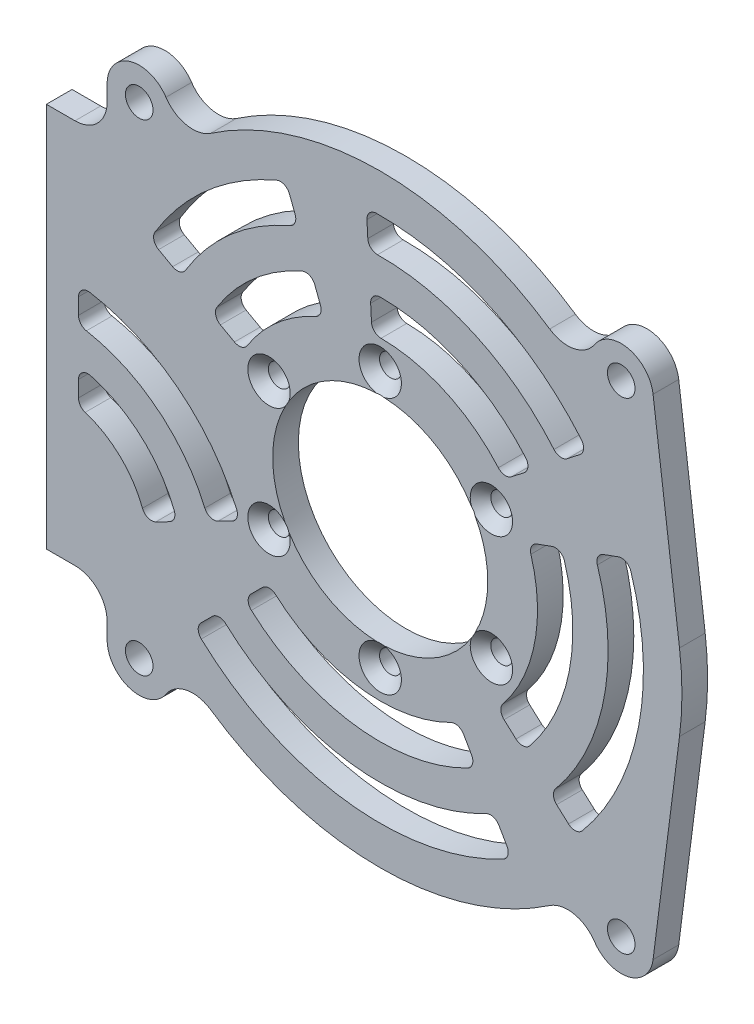
SolidWorks part; units mm, degrees
material "Thornel Mat VMA"
ref_plane "前视基准面" through (0, 0, 0) normal (0, 0, 1) x (1, 0, 0)
ref_plane "上视基准面" through (0, 0, 0) normal (0, 1, 0) x (1, 0, 0)
ref_plane "右视基准面" through (0, 0, 0) normal (1, 0, 0) x (0, 0, -1)
sketch "草图1" plane through (0, 0, 0) normal (0, 0, 1) x (1, 0, 0)
  line L0 (0, 0) -> (50000, 0) construction
  line L1 (-52, 8.75) -> (-52, -8.75)
  line L2 (-52, 8.75) -> (-52, 30)
  line L3 (-52, -8.75) -> (-52, -30)
  line L6 (-42.54, 37.5) -> (-42.54, 35)
  line L7 (-47.54, 30) -> (-52, 30)
  line L8 (-47.54, -30) -> (-52, -30)
  line L9 (-42.54, -37.5) -> (-42.54, -35)
  line L10 (0, 0) -> (0, -50000) construction
  line L11 (42.4995, 38.1352) -> (46.6192, 5.9711)
  line L12 (42.4995, -38.1352) -> (46.6192, -5.9711)
  circle A2 centre (-37.54, 37.5) radius 2.15
  circle A3 centre (-37.54, -37.5) radius 2.15
  arc A4 (-33.3722, 40.2622) -> (-42.54, 37.5) centre (-37.54, 37.5) ccw
  arc A5 (-42.54, -37.5) -> (-33.3722, -40.2622) centre (-37.54, -37.5) ccw
  arc A6 (-26.3963, -38.8874) -> (26.3963, -38.8874) centre (0, 0) ccw
  arc A7 (-33.3722, 40.2622) -> (-26.3963, 38.8874) centre (-29.2045, 43.0244) ccw
  arc A8 (-33.3722, -40.2622) -> (-42.54, -37.5) centre (-37.54, -37.5) cw
  arc A9 (-33.3722, -40.2622) -> (-26.3963, -38.8874) centre (-29.2045, -43.0244) cw
  circle A10 centre (37.54, -37.5) radius 2.15
  circle A11 centre (37.54, 37.5) radius 2.15
  arc A12 (42.4995, 38.1352) -> (33.3722, 40.2622) centre (37.54, 37.5) ccw
  arc A13 (33.3722, -40.2622) -> (42.4995, -38.1352) centre (37.54, -37.5) ccw
  arc A14 (33.3722, 40.2622) -> (26.3963, 38.8874) centre (29.2045, 43.0244) cw
  arc A15 (33.3722, -40.2622) -> (26.3963, -38.8874) centre (29.2045, -43.0244) ccw
  arc A16 (26.3963, 38.8874) -> (-26.3963, 38.8874) centre (0, 0) ccw
  arc A17 (46.6192, -5.9711) -> (46.6192, 5.9711) centre (0, 0) ccw
  arc A18 (-47.54, -30) -> (-42.54, -35) centre (-47.54, -35) cw
  arc A19 (-42.54, 35) -> (-47.54, 30) centre (-47.54, 35) cw
  point P8 (-52, 0)
  point P44 (-42.54, -30)
  point P47 (-42.54, 30)
  dimension "D5" = 4.3
  dimension "D6" = 75
  dimension "D8" = 10
  dimension "D9" = 94
  dimension "D10" = 5
  dimension "D11" = 10
  dimension "D12" = 5
  dimension "D13" = 5
  dimension "D14" = 5
  dimension "D2" = 17.5
  dimension "D3" = 52
  dimension "D4" = 60
  dimension "D7" = 14.46
extrude "凸台-拉伸1" add sketch "草图1" along normal blind 4
sketch "草图2" plane through (0, 0, 4) normal (0, 0, 1) x (1, 0, 0)
  circle A1 centre (0, 0) radius 16.75
  arc A2 (26.3963, 38.8874) -> (-26.3963, 38.8874) centre (0, 0) ccw construction
  circle A3 centre (0, 0) radius 20 construction
  circle A4 centre (0, 20) radius 1.65
  circle A5 centre (17.3205, 10) radius 1.65
  circle A6 centre (17.3205, -10) radius 1.65
  circle A7 centre (0, -20) radius 1.65
  circle A8 centre (-17.3205, -10) radius 1.65
  circle A9 centre (-17.3205, 10) radius 1.65
  point P21 (0, 0)
  dimension "D1" = 33.5
  dimension "D2" = 40
  dimension "D3" = 3.3
  dimension "D4" = 6
extrude "切除-拉伸1" cut sketch "草图2" against normal blind 10
sketch "草图3" plane through (0, 0, 4) normal (0, 0, 1) x (1, 0, 0)
  line L0 (-8.78, 22.8727) -> (0, 0) construction
  line L1 (0, 0) -> (-1.2822, 24.4664) construction
  line L2 (19.3063, 15.0837) -> (0, 0) construction
  line L3 (0, 0) -> (23.0225, 8.3795) construction
  line L4 (18.207, -16.3937) -> (0, 0) construction
  line L5 (0, 0) -> (12.25, -21.2176) construction
  line L6 (-8.78, 22.8727) -> (-10.751, 28.0074)
  line L7 (-1.2822, 24.4664) -> (-1.5701, 29.9589)
  line L8 (19.3063, 15.0837) -> (23.6403, 18.4698)
  line L9 (23.0225, 8.3795) -> (28.1908, 10.2606)
  line L10 (12.25, -21.2176) -> (15, -25.9808)
  line L11 (18.207, -16.3937) -> (22.2943, -20.0739)
  line L12 (0, 0) -> (50000, 0) construction
  line L13 (0, 0) -> (0, -50000) construction
  line L14 (-21.4282, 11.8778) -> (0, 0) construction
  line L15 (-21.4282, 11.8778) -> (-26.2386, 14.5443)
  line L16 (-21.8297, -11.1228) -> (0, 0) construction
  line L17 (0, 0) -> (-17.3241, -17.3241) construction
  line L18 (-21.8297, -11.1228) -> (-26.7302, -13.6197)
  line L19 (-17.3241, -17.3241) -> (-21.2132, -21.2132)
  line L20 (-52, -30) -> (-52, 30) construction
  line L21 (-47, 8.25) -> (-47, 2.75)
  line L22 (-12.7221, 33.1421) -> (-14.6931, 38.2768)
  line L23 (-31.049, 17.2107) -> (-35.8594, 19.8772)
  line L24 (-1.8579, 35.4513) -> (-2.1458, 40.9438)
  line L25 (27.9744, 21.856) -> (32.3084, 25.2421)
  line L26 (33.3591, 12.1417) -> (38.5274, 14.0228)
  line L27 (26.3816, -23.7541) -> (30.4689, -27.4344)
  line L28 (17.75, -30.7439) -> (20.5, -35.507)
  line L29 (-25.1023, -25.1023) -> (-28.9914, -28.9914)
  line L30 (-31.6307, -16.1167) -> (-36.5313, -18.6136)
  line L31 (-47, -2.75) -> (-47, -8.25)
  arc A0 (-8.78, 22.8727) -> (-21.4282, 11.8778) centre (0, 0) ccw construction
  arc A1 (-8.78, 22.8727) -> (-21.4282, 11.8778) centre (0, 0) ccw
  arc A2 (-10.751, 28.0074) -> (-26.2386, 14.5443) centre (0, 0) ccw
  arc A3 (-12.7221, 33.1421) -> (-31.049, 17.2107) centre (0, 0) ccw
  arc A4 (-14.6931, 38.2768) -> (-35.8594, 19.8772) centre (0, 0) ccw
  arc A5 (19.3063, 15.0837) -> (-1.2822, 24.4664) centre (0, 0) ccw construction
  arc A6 (19.3063, 15.0837) -> (-1.2822, 24.4664) centre (0, 0) ccw
  arc A7 (23.6403, 18.4698) -> (-1.5701, 29.9589) centre (0, 0) ccw
  arc A8 (27.9744, 21.856) -> (-1.8579, 35.4513) centre (0, 0) ccw
  arc A9 (32.3084, 25.2421) -> (-2.1458, 40.9438) centre (0, 0) ccw
  arc A10 (30.4689, -27.4344) -> (38.5274, 14.0228) centre (0, 0) ccw
  arc A11 (26.3816, -23.7541) -> (33.3591, 12.1417) centre (0, 0) ccw
  arc A12 (22.2943, -20.0739) -> (28.1908, 10.2606) centre (0, 0) ccw
  arc A13 (18.207, -16.3937) -> (23.0225, 8.3795) centre (0, 0) ccw construction
  arc A14 (18.207, -16.3937) -> (23.0225, 8.3795) centre (0, 0) ccw
  arc A15 (-17.3241, -17.3241) -> (12.25, -21.2176) centre (0, 0) ccw construction
  arc A16 (-17.3241, -17.3241) -> (12.25, -21.2176) centre (0, 0) ccw
  arc A17 (-21.2132, -21.2132) -> (15, -25.9808) centre (0, 0) ccw
  arc A18 (-25.1023, -25.1023) -> (17.75, -30.7439) centre (0, 0) ccw
  arc A19 (-28.9914, -28.9914) -> (20.5, -35.507) centre (0, 0) ccw
  arc A21 (-47, -8.25) -> (-36.5313, -18.6136) centre (-50.2216, -21.9735) cw
  arc A22 (-47, -2.75) -> (-31.6307, -16.1167) centre (-50.2216, -21.9735) cw
  arc A24 (-47, 2.75) -> (-26.7302, -13.6197) centre (-50.2216, -21.9735) cw
  arc A25 (-47, 8.25) -> (-21.8297, -11.1228) centre (-50.2216, -21.9735) cw
  dimension "D1" = 49
  dimension "D2" = 82
  dimension "D3" = 5.5
  dimension "D4" = 5.5
  dimension "D5" = 18
  dimension "D6" = 18
  dimension "D7" = 18
  dimension "D8" = 40
  dimension "D9" = 3
  dimension "D10" = 20
  dimension "D11" = 30
  dimension "D12" = 45
  dimension "D13" = 18
  dimension "D14" = 5
  dimension "D15" = 16.5
  dimension "D16" = 5.5
  dimension "D17" = 5.5
extrude "切除-拉伸2" cut sketch "草图3" against normal blind 10
fillet "圆角1" radius 1.5 40 edges at (-14.6931, 38.2768, 2) (18.207, -16.3937, 2) (23.0225, 8.3795, 2) (28.1908, 10.2606, 2) (22.2943, -20.0739, 2) (-47, -2.75, 2) (-31.6307, -16.1167, 2) (-36.5313, -18.6136, 2) (-47, -8.25, 2) (-26.2386, 14.5443, 2) (-10.751, 28.0074, 2) (-8.78, 22.8727, 2) (-21.4282, 11.8778, 2) (-2.1458, 40.9438, 2) (32.3084, 25.2421, 2) (27.9744, 21.856, 2) (-1.8579, 35.4513, 2) (38.5274, 14.0228, 2) (30.4689, -27.4344, 2) (26.3816, -23.7541, 2) (33.3591, 12.1417, 2) (19.3063, 15.0837, 2) (-1.2822, 24.4664, 2) (-1.5701, 29.9589, 2) (23.6403, 18.4698, 2) (-25.1023, -25.1023, 2) (17.75, -30.7439, 2) (20.5, -35.507, 2) (-28.9914, -28.9914, 2) (15, -25.9808, 2) (-21.2132, -21.2132, 2) (-17.3241, -17.3241, 2) (12.25, -21.2176, 2) (-12.7221, 33.1421, 2) (-31.049, 17.2107, 2) (-35.8594, 19.8772, 2) (-26.7302, -13.6197, 2) (-47, 2.75, 2) (-47, 8.25, 2) (-21.8297, -11.1228, 2)
hole_wizard "打孔尺寸(%根据十字)槽半沉头木螺钉的类型1" positions "3D草图2" profile "草图6" countersink size "M3" standard "GB" end condition through all
sketch3d "3D草图2"
  line L0 (-17.3205, 10, 0) -> (-17.3205, 10, 4) construction
  line L1 (0, 20, 0) -> (0, 20, 4) construction
  line L2 (17.3205, 10, 0) -> (17.3205, 10, 4) construction
  line L3 (17.3205, -10, 0) -> (17.3205, -10, 4) construction
  line L4 (0, -20, 0) -> (0, -20, 4) construction
  line L5 (-17.3205, -10, 0) -> (-17.3205, -10, 4) construction
  point P0 (-17.3205, 10, 4)
  point P4 (0, 20, 4)
  point P8 (17.3205, 10, 4)
  point P12 (17.3205, -10, 4)
  point P16 (0, -20, 4)
  point P20 (-17.3205, -10, 4)
sketch "草图6" plane through (-17.3205, 10, 4) normal (1, 0, 0) x (0, -1, 0)
  line L0 (0, 0) -> (0, 4)
  line L1 (0, 4) -> (1.7, 4)
  line L2 (1.7, 4) -> (1.7, 1.6)
  line L3 (1.7, 1.6) -> (3.3, 0)
  line L5 (3.3, 0) -> (0, 0)
  line L6 (-1.7, 1.6) -> (-3.3, 0) construction
  line L11 (0, -6.35) -> (0, 107.95) construction
  dimension "通孔孔直径" = 3.4
  dimension "通孔孔深度" = 4
  dimension "近端锥形沉头孔直径" = 6.6
  dimension "近端锥形沉头孔角度" = 90
